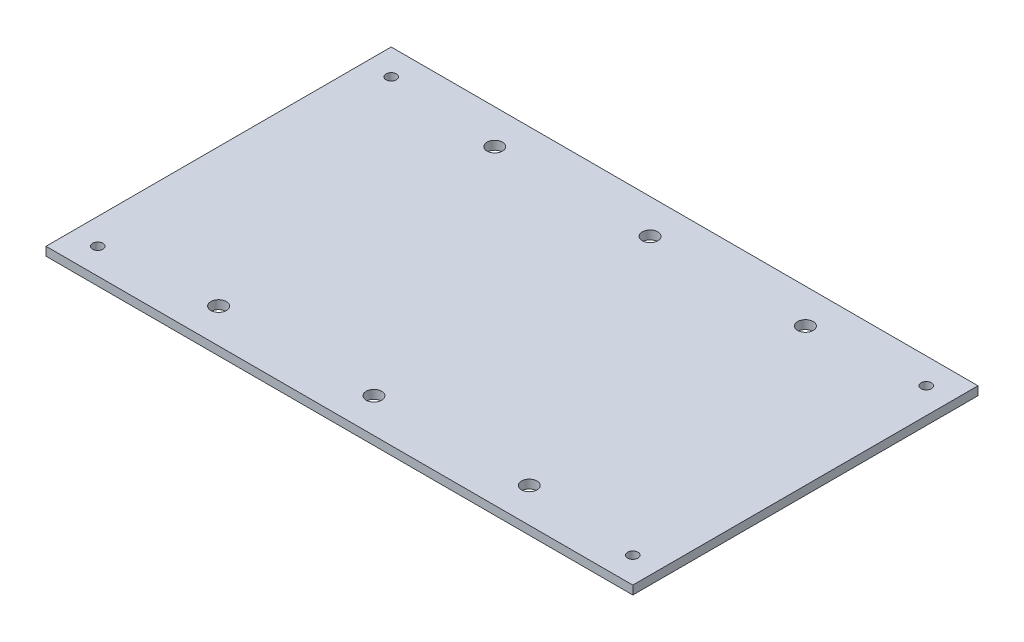
SolidWorks part; units mm, degrees
ref_plane "Front Plane" through (0, 0, 0) normal (0, 0, 1) x (1, 0, 0)
ref_plane "Top Plane" through (0, 0, 0) normal (0, 1, 0) x (1, 0, 0)
ref_plane "Right Plane" through (0, 0, 0) normal (1, 0, 0) x (0, 0, -1)
sketch "Sketch1" plane through (0, 0, 0) normal (0, 1, 0) x (1, 0, 0)
  line L0 (0, -1000) -> (0, 49000) construction
  line L1 (-170, 100) -> (170, 100)
  line L2 (-170, 100) -> (-170, -100)
  line L3 (-170, -100) -> (170, -100)
  line L4 (170, 100) -> (170, -100)
  line L5 (-170, 100) -> (170, -100) construction
  line L6 (-170, -100) -> (170, 100) construction
  line L7 (-1000, 0) -> (49000, 0) construction
  circle A0 centre (155, 85) radius 3
  circle A1 centre (-155, 85) radius 3
  circle A2 centre (-155, -85) radius 3
  circle A3 centre (155, -85) radius 3
  circle A4 centre (0, 80) radius 4.5
  circle A5 centre (0, -80) radius 4.5
  circle A6 centre (90, 80) radius 4.5
  circle A7 centre (90, -80) radius 4.5
  circle A8 centre (-90, -80) radius 4.5
  circle A9 centre (-90, 80) radius 4.5
  point P0 (0, 0)
  dimension "D3" = 15
  dimension "D5" = 6
  dimension "D7" = 9
  dimension "D9" = 90
  dimension "D1" = 340
  dimension "D2" = 200
  dimension "D4" = 15
  dimension "D6" = 20
  dimension "D8" = 2
extrude "Boss-Extrude1" add sketch "Sketch1" along normal blind 5
